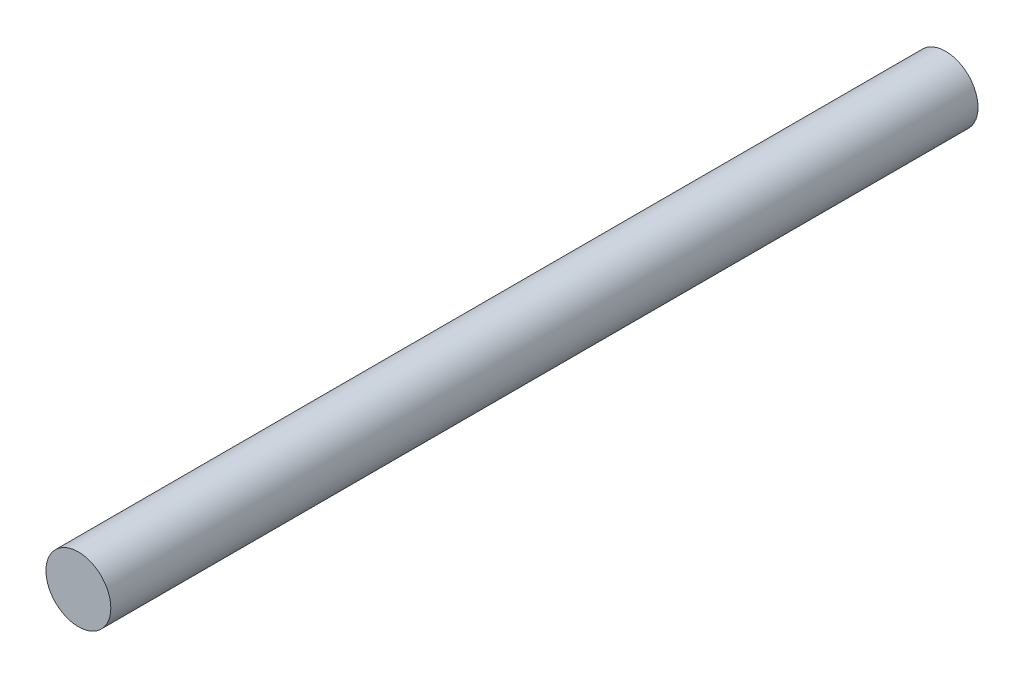
SolidWorks part; units mm, degrees
material "1060 Alloy"
ref_plane "Front" through (0, 0, 0) normal (0, 0, 1) x (1, 0, 0)
ref_plane "Top" through (0, 0, 0) normal (0, 1, 0) x (1, 0, 0)
ref_plane "Right" through (0, 0, 0) normal (1, 0, 0) x (0, 0, -1)
sketch "Sketch1" plane through (0, 0, 0) normal (0, 0, 1) x (1, 0, 0)
  circle A0 centre (-38.1, 0.127) radius 2.3749
  arc A1 (-35.7612, 0.5394) -> (-36.0681, -1.1025) centre (-38.1, 0.127) ccw construction
extrude "Extrude1" add sketch "Sketch1" against normal up to surface (63.5 mm away)
